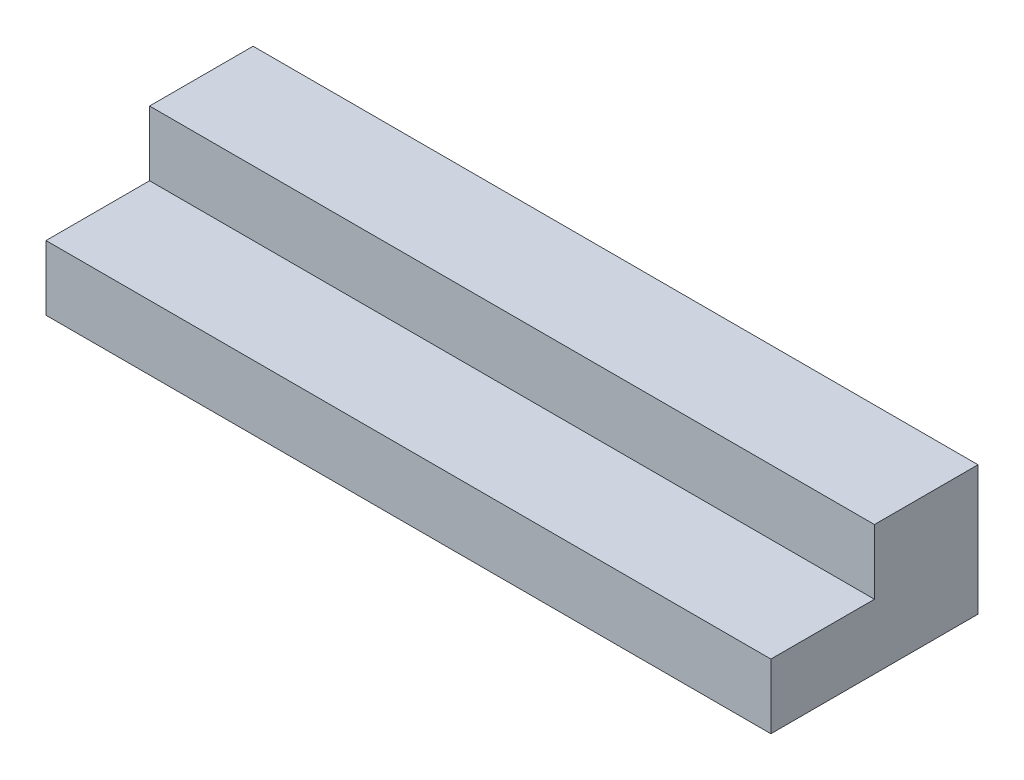
SolidWorks part; units mm, degrees
ref_plane "前视基准面" through (0, 0, 0) normal (0, 0, 1) x (1, 0, 0)
ref_plane "上视基准面" through (0, 0, 0) normal (0, 1, 0) x (1, 0, 0)
ref_plane "右视基准面" through (0, 0, 0) normal (1, 0, 0) x (0, 0, -1)
sketch "草图1" plane through (0, 0, 0) normal (1, 0, 0) x (0, 0, -1)
  line L0 (178.2946, 136.6566) -> (178.2946, -113.3434)
  line L1 (178.2946, -113.3434) -> (-221.7054, -113.3434)
  line L2 (-221.7054, -113.3434) -> (-221.7054, 11.6566)
  line L3 (-221.7054, 11.6566) -> (-21.7054, 11.6566)
  line L4 (-21.7054, 136.6566) -> (178.2946, 136.6566)
  line L5 (-21.7054, 136.6566) -> (-21.7054, 11.6566)
extrude "凸台-拉伸1" add sketch "草图1" along normal blind 1400
